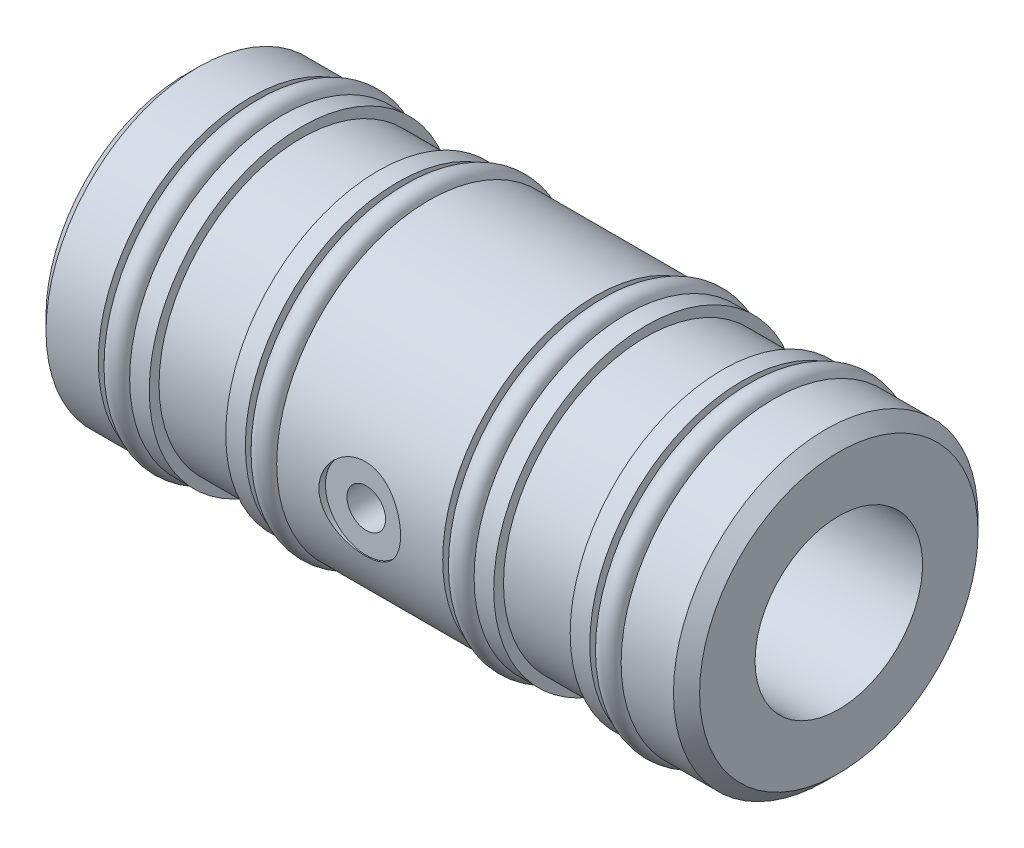
SolidWorks part; units mm, degrees
ref_plane "Front Plane" through (0, 0, 0) normal (0, 0, 1) x (1, 0, 0)
ref_plane "Top Plane" through (0, 0, 0) normal (0, 1, 0) x (1, 0, 0)
ref_plane "Right Plane" through (0, 0, 0) normal (1, 0, 0) x (0, 0, -1)
sketch "Sketch1" plane through (0, 0, 0) normal (0, 0, 1) x (1, 0, 0)
  line L0 (0, 6.51) -> (50.8, 6.51)
  line L1 (50.8, 6.51) -> (50.8, 11.835)
  line L2 (50.8, 11.835) -> (45.718, 11.835)
  line L3 (45.718, 11.835) -> (45.718, 10.615)
  line L4 (45.718, 10.615) -> (43.28, 10.615)
  line L5 (43.28, 10.615) -> (43.28, 11.835)
  line L6 (43.28, 11.835) -> (41.7576, 11.835)
  line L7 (41.7576, 11.835) -> (41.7576, 11.075)
  line L8 (0, 6.51) -> (0, 11.835)
  line L9 (0, 11.835) -> (5.08, 11.835)
  line L10 (5.08, 11.835) -> (5.08, 10.615)
  line L11 (5.08, 10.615) -> (7.518, 10.615)
  line L12 (7.518, 10.615) -> (7.518, 11.835)
  line L13 (7.518, 11.835) -> (9.0424, 11.835)
  line L14 (9.0424, 11.835) -> (9.0424, 11.075)
  line L15 (9.0424, 11.075) -> (14.986, 11.075)
  line L16 (14.986, 11.075) -> (14.986, 11.835)
  line L17 (14.986, 11.835) -> (16.51, 11.835)
  line L18 (16.51, 11.835) -> (16.51, 10.615)
  line L19 (16.51, 10.615) -> (18.948, 10.615)
  line L20 (18.948, 10.615) -> (18.948, 11.835)
  line L21 (18.948, 11.835) -> (31.85, 11.835)
  line L22 (31.85, 11.835) -> (31.85, 10.615)
  line L23 (41.7576, 11.075) -> (35.814, 11.075)
  line L24 (35.814, 11.075) -> (35.814, 11.835)
  line L25 (35.814, 11.835) -> (34.288, 11.835)
  line L26 (34.288, 11.835) -> (34.288, 10.615)
  line L27 (34.288, 10.615) -> (31.85, 10.615)
  line L28 (0, 0) -> (50.8, 0) construction
  dimension "Bore ID" = 13.02
  dimension "OAL" = 50.8
  dimension "Moglice groove width" = 5.9436
  dimension "O-ring groove width" = 2.438
  dimension "Edge to 1st o-ring groove" = 5.08
  dimension "Edge to 2nd o-ring groove" = 16.51
  dimension "Bushing OD" = 23.67
  dimension "O-ring groove dia" = 21.23
  dimension "Edge to 3rd o-ring groove" = 31.85
  dimension "edge to 4th o-ring groove" = 43.28
  dimension "Edge to 1st moglice groove" = 9.0424
  dimension "Edge to 2nd moglice groove" = 35.814
  dimension "Moglice Groove Dia" = 22.15
revolve "Revolve1" add sketch "Sketch1" angle 360 about L28
chamfer "Chamfer1" distance 1.016 angle 45 2 edges at (0, 0, 11.835) (50.8, 0, 11.835)
ref_plane "Plane1" through (0, 0, -7.9121) normal (0, 0, 1) x (1, 0, 0)
hole_wizard "1/4 (0.25) Diameter Hole1" positions "3DSketch1" profile "Sketch2" hole size "1/4" standard "Ansi Inch"
sketch3d "3DSketch1"
  point P0 (25.4, 0, 11.835)
  dimension "Edge to air hole" = 25.4
sketch "Sketch2" plane through (25.4, 0, 11.835) normal (1, 0, 0) x (0, -1, 0)
  line L0 (0, 0) -> (0, 0.51)
  line L1 (0, 0.51) -> (3.175, 0.51)
  line L2 (3.175, 0.51) -> (3.175, 0)
  line L5 (3.175, 0) -> (0, 0)
  line L10 (0, 0.51) -> (-3.175, 0.51) construction
  line L11 (0, -6.35) -> (0, 107.95) construction
  dimension "Hole Dia." = 6.35
  dimension "Hole Depth" = 0.51
  dimension "Drill Angle" = 180
hole_wizard "Air Hole" positions "Sketch4" profile "Sketch3" tap size "M3x0.5" standard "Ansi Metric"
sketch "Sketch4" plane through (0, 0, 11.325) normal (0, 0, 1) x (1, 0, 0)
  circle A0 centre (25.4, 0) radius 3.175 construction
  point P0 (25.4, 0)
sketch "Sketch3" plane through (25.4, 0, 11.325) normal (1, 0, 0) x (0, -1, 0)
  line L0 (0, 0) -> (0, 7.0978)
  line L1 (0, 7.0978) -> (1.2446, 6.35)
  line L2 (1.2446, 6.35) -> (1.2446, 5.99)
  line L3 (1.2446, 5.99) -> (1.5, 5.99)
  line L4 (1.5, 5.99) -> (1.5, 0)
  line L5 (1.5, 0) -> (0, 0)
  line L10 (0, 7.0978) -> (-1.2446, 6.35) construction
  line L11 (0, -6.35) -> (0, 107.95) construction
  dimension "Tap Drill Dia." = 2.4892
  dimension "Tap Drill Depth" = 6.35
  dimension "Thread Major Dia." = 3
  dimension "Thread Depth" = 5.99
  dimension "Drill Angle" = 118
sketch "Sketch5" plane through (0, 0, 0) normal (0, 0, 1) x (1, 0, 0)
  line L0 (5.08, 10.615) -> (7.518, 10.615) construction
  line L3 (7.518, 11.835) -> (7.518, -11.835) construction
  line L4 (18.948, 11.835) -> (18.948, -11.835) construction
  line L5 (31.85, -11.835) -> (31.85, 11.835) construction
  line L6 (43.28, -11.835) -> (43.28, 11.835) construction
  line L7 (0, 0) -> (51.7691, 0) construction
  circle A0 centre (44.5, 11.3737) radius 0.8763
  circle A1 centre (33.07, 11.3737) radius 0.8763
  circle A2 centre (17.728, 11.3737) radius 0.8763
  circle A3 centre (6.2988, 11.3737) radius 0.8763
  dimension "D1" = 1.7526
  dimension "D2" = 0.7587
  dimension "D6" = 1.22
  dimension "D3" = 1.2192
  dimension "D4" = 1.22
  dimension "D5" = 1.22
revolve "Revolve2" add sketch "Sketch5" angle 360 about L7
equation "\"plane offset\"= \"Bushing OD@Sketch1\" / 2"
